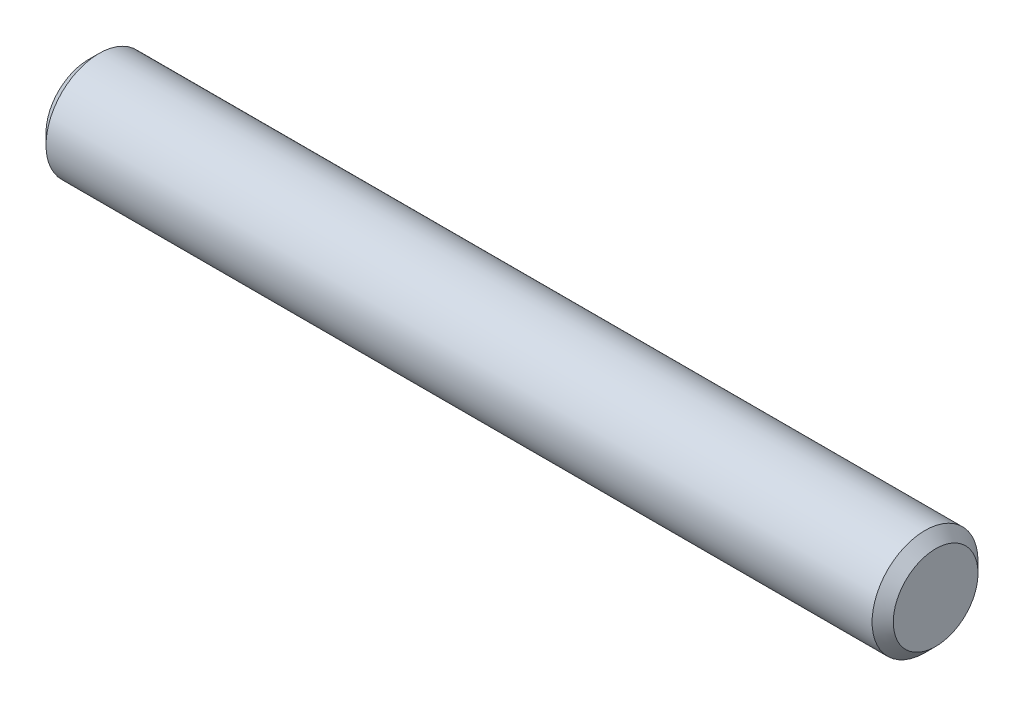
SolidWorks part; units mm, degrees
ref_plane "Front Plane" through (0, 0, 0) normal (0, 0, 1) x (1, 0, 0)
ref_plane "Top Plane" through (0, 0, 0) normal (0, 1, 0) x (1, 0, 0)
ref_plane "Right Plane" through (0, 0, 0) normal (1, 0, 0) x (0, 0, -1)
sketch "Sketch1" plane through (0, 0, 0) normal (0, 0, 1) x (1, 0, 0)
  line L0 (-6.35, 0) -> (6.35, 0) construction
  line L1 (-6.35, 0.7937) -> (-6.35, -0.7937) construction
  line L2 (6.35, 0.7937) -> (6.35, -0.7937) construction
  dimension "Diameter" = 1.5875
  dimension "Length" = 12.7
sketch "Sketch2" plane through (0, 0, 0) normal (1, 0, 0) x (0, 0, -1)
  circle A0 centre (0, 0) radius 0.7937
extrude "Extrude1" add sketch "Sketch2" against normal up to vertex (6.35 mm away) and the other way up to vertex (6.35 mm away) up to point (-6.35, 0, 0) other way up to point (6.35, 0, 0)
chamfer "Chamfer1" distance 0.1588 angle 45 2 edges at (6.35, 0, -0.7937) (-6.35, 0, -0.7937)
equation "\"D1@Chamfer1\" = \"Diameter@Sketch1\"*.1"
